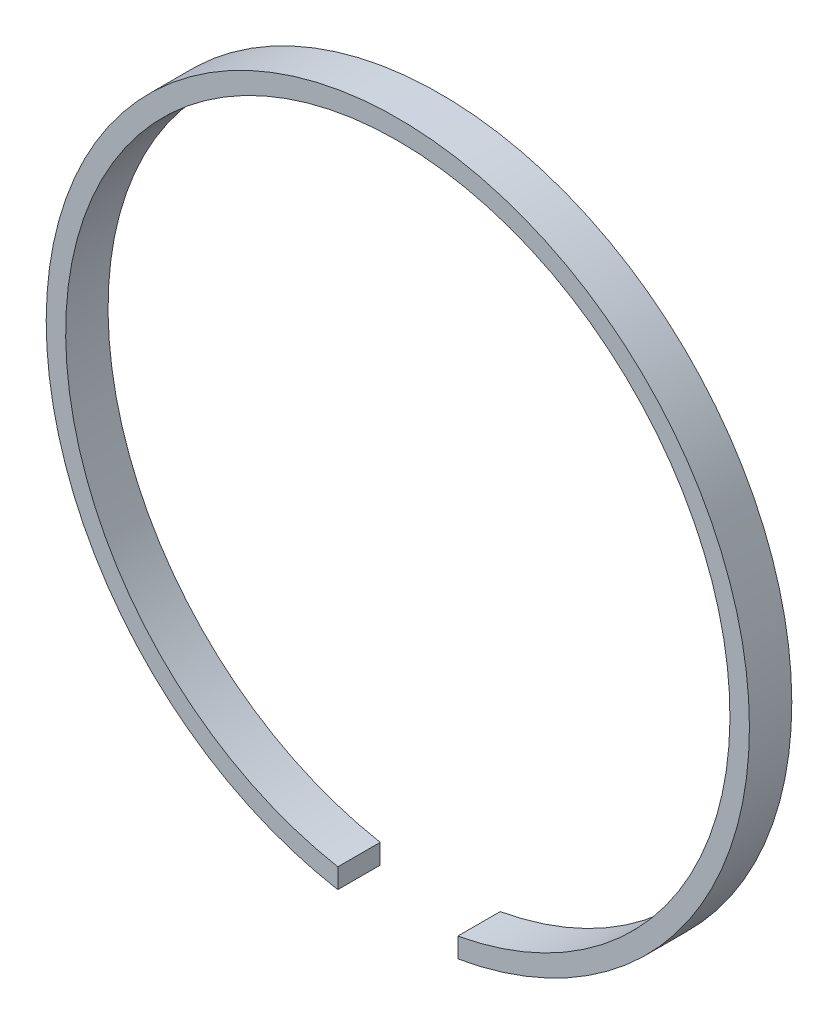
SolidWorks part; units mm, degrees
ref_plane "Front Plane" through (0, 0, 0) normal (0, 0, 1) x (1, 0, 0)
ref_plane "Top Plane" through (0, 0, 0) normal (0, 1, 0) x (1, 0, 0)
ref_plane "Right Plane" through (0, 0, 0) normal (1, 0, 0) x (0, 0, -1)
sketch "Sketch1" plane through (0, 0, 0) normal (0, 0, 1) x (1, 0, 0)
  circle A0 centre (0, 0) radius 29
  circle A1 centre (0, 0) radius 30.7
  dimension "D1" = 58
  dimension "D2" = 1.7
extrude "Boss-Extrude1" add sketch "Sketch1" along normal blind 3.7
sketch "Sketch2" plane through (0, 0, 0) normal (0, 1, 0) x (1, 0, 0)
  line L1 (-5.2372, 10.3498) -> (5.2372, 10.3498)
  line L2 (-5.2372, 10.3498) -> (-5.2372, -10.3498)
  line L3 (-5.2372, -10.3498) -> (5.2372, -10.3498)
  line L4 (5.2372, 10.3498) -> (5.2372, -10.3498)
  line L5 (-5.2372, 10.3498) -> (5.2372, -10.3498) construction
  line L6 (-5.2372, -10.3498) -> (5.2372, 10.3498) construction
  point P0 (0, 0)
extrude "Cut-Extrude1" cut sketch "Sketch2" against normal blind 58
